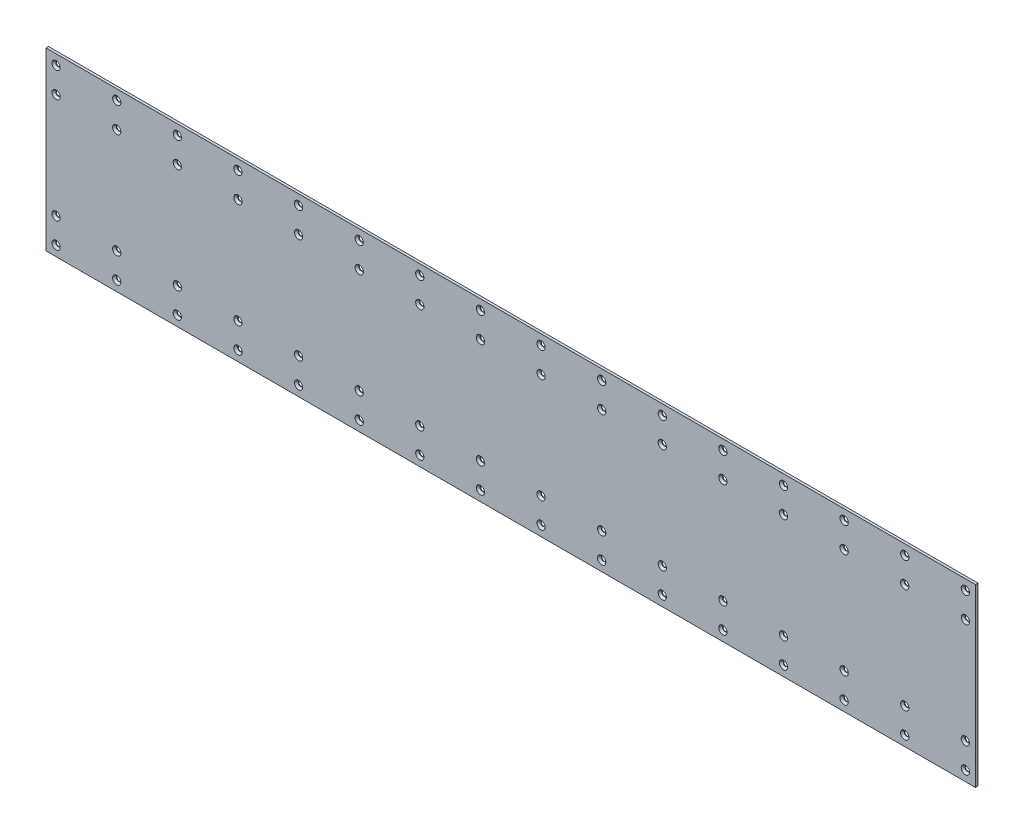
SolidWorks part; units mm, degrees
material "6061-T4 (SS)"
ref_plane "Front Plane" through (0, 0, 0) normal (0, 0, 1) x (1, 0, 0)
ref_plane "Top Plane" through (0, 0, 0) normal (0, 1, 0) x (1, 0, 0)
ref_plane "Right Plane" through (0, 0, 0) normal (1, 0, 0) x (0, 0, -1)
sketch "Sketch1" plane through (0, 0, 0) normal (0, 0, 1) x (1, 0, 0)
  line L1 (0, 0) -> (1168.4, 0)
  line L2 (0, 0) -> (0, 220.98)
  line L3 (0, 220.98) -> (1168.4, 220.98)
  line L4 (1168.4, 0) -> (1168.4, 220.98)
  dimension "D1" = 1168.4
  dimension "D2" = 220.98
extrude "Boss-Extrude1" add sketch "Sketch1" against normal blind 3.175
sketch "Sketch2" plane through (0, 0, 0) normal (0, 0, 1) x (1, 0, 0)
  line L0 (12.7, 208.28) -> (1155.7, 208.28) construction
  line L1 (12.7, 176.53) -> (1155.7, 176.53) construction
  line L2 (12.7, 44.45) -> (1155.7, 44.45) construction
  line L3 (12.7, 12.7) -> (1155.7, 12.7) construction
  line L4 (0, 220.98) -> (0, 0) construction
  line L5 (1168.4, 220.98) -> (0, 220.98) construction
  line L6 (0, 0) -> (1168.4, 0) construction
  dimension "D1" = 12.7
  dimension "D2" = 12.7
  dimension "D3" = 12.7
  dimension "D4" = 31.75
  dimension "D5" = 31.75
  dimension "D6" = 1143
hole_wizard "CSK for #0 Flat Head Machine Screw (100)1" positions "3DSketch1" profile "Sketch3" countersink size "#0" standard "ANSI Inch" end condition through all
sketch3d "3DSketch1"
  point P0 (12.7, 208.28, 0)
  point P3 (12.7, 176.53, 0)
  point P6 (12.7, 44.45, 0)
  point P9 (12.7, 12.7, 0)
sketch "Sketch3" plane through (12.7, 208.28, 0) normal (1, 0, 0) x (0, -1, 0)
  line L0 (0, 0) -> (0, 3.175)
  line L1 (0, 3.175) -> (2.7559, 3.175)
  line L2 (2.7559, 3.175) -> (2.7559, 2.4384)
  line L3 (2.7559, 2.4384) -> (5.1943, 0)
  line L5 (5.1943, 0) -> (0, 0)
  line L6 (-2.7559, 2.4384) -> (-5.1943, 0) construction
  line L11 (0, -6.35) -> (0, 107.95) construction
  dimension "Thru Hole Dia." = 5.5118
  dimension "Thru Hole Depth" = 3.175
  dimension "Near C'Sink Dia." = 10.3886
  dimension "Near C'Sink Angle" = 90
pattern_linear "LPattern1" count 16 spacing 76.2 along (1, 0, 0) of "CSK for #0 Flat Head Machine Screw (100)1"
